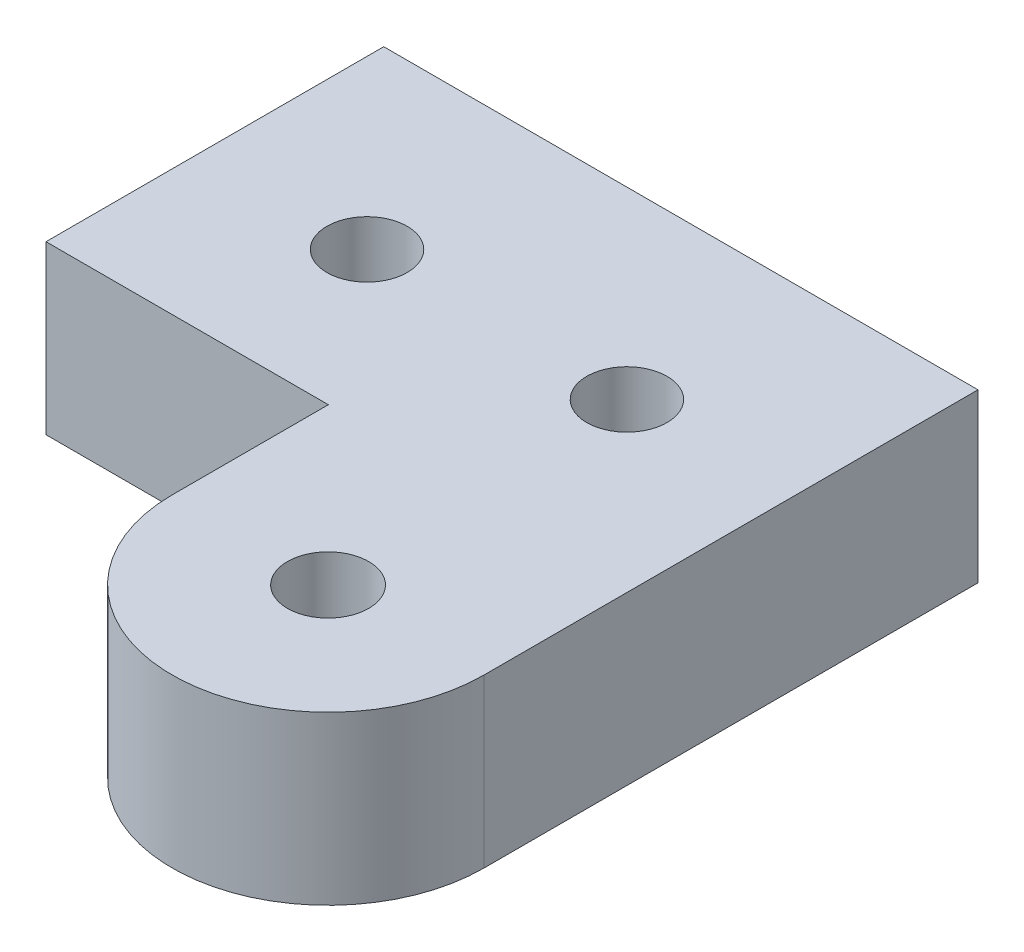
SolidWorks part; units mm, degrees
ref_plane "Front Plane" through (0, 0, 0) normal (0, 0, 1) x (1, 0, 0)
ref_plane "Top Plane" through (0, 0, 0) normal (0, 1, 0) x (1, 0, 0)
ref_plane "Right Plane" through (0, 0, 0) normal (1, 0, 0) x (0, 0, -1)
sketch "Sketch1" plane through (0, 0, 0) normal (0, 1, 0) x (1, 0, 0)
  line L0 (4.9589, -28.2781) -> (4.9589, -16.2781)
  line L1 (-4.3685, -28.2781) -> (-4.3685, -23.6056)
  line L3 (-12.8127, -16.2781) -> (-12.8127, -23.6056)
  line L4 (-12.8127, -23.6056) -> (-4.3685, -23.6056)
  line L5 (4.9589, -16.2781) -> (4.9589, -13.5051)
  line L6 (4.9589, -13.5051) -> (-12.8127, -13.5051)
  line L7 (-12.8127, -13.5051) -> (-12.8127, -16.2781)
  arc A0 (-4.3685, -28.2781) -> (4.9589, -28.2781) centre (0.2952, -28.2781) ccw
extrude "Boss-Extrude1" add sketch "Sketch1" along normal blind 5
sketch "Sketch2" plane through (0, 0, 0) normal (0, -1, 0) x (1, 0, 0)
  line L0 (-4.3685, 24.3051) -> (4.9589, 24.3051)
  line L1 (-4.3685, 23.6056) -> (-4.3685, 28.2781) construction
  line L2 (4.9589, 28.2781) -> (4.9589, 13.5051) construction
  line L3 (4.9589, 13.5051) -> (-12.8127, 13.5051) construction
  dimension "D1" = 10.8
sketch "Sketch3" plane through (0, 5, 0) normal (0, 1, 0) x (1, 0, 0)
  line L0 (-4.3685, -24.3051) -> (5.0728, -24.3051)
  line L1 (-4.3685, -23.6056) -> (-4.3685, -28.2781) construction
  line L2 (4.9589, -13.5051) -> (-12.8127, -13.5051) construction
  dimension "D1" = 10.8
hole_wizard "M2 Clearance Hole1" positions "Sketch5" profile "Sketch4" hole size "M2" standard "ANSI Metric"
sketch "Sketch5" plane through (0, 5, 0) normal (0, 1, 0) x (1, 0, 0)
  line L0 (4.9589, -13.5051) -> (-12.8127, -13.5051) construction
  line L1 (-12.8127, -13.5051) -> (-12.8127, -23.6056) construction
  line L2 (4.9589, -28.2781) -> (4.9589, -13.5051) construction
  point P0 (-0.0411, -19.0051)
  point P2 (-7.8127, -19.0051)
  dimension "D1" = 5.5
  dimension "D2" = 5.5
  dimension "D3" = 5
  dimension "D4" = 5
sketch "Sketch4" plane through (-0.0411, 5, 19.0051) normal (1, 0, 0) x (0, 0, 1)
  line L0 (0, 0) -> (0, 12.721)
  line L1 (0, 12.721) -> (1.2, 12)
  line L2 (1.2, 12) -> (1.2, 0)
  line L5 (1.2, 0) -> (0, 0)
  line L10 (0, 12.721) -> (-1.2, 12) construction
  line L11 (0, -6.35) -> (0, 107.95) construction
  dimension "Hole Dia." = 2.4
  dimension "Hole Depth" = 12
  dimension "Drill Angle" = 118
sketch "Sketch6" plane through (0, 5, 0) normal (0, 1, 0) x (1, 0, 0)
  circle A0 centre (0.2952, -28.2781) radius 1.215
extrude "Cut-Extrude1" cut sketch "Sketch6" against normal blind 10 contours A0
